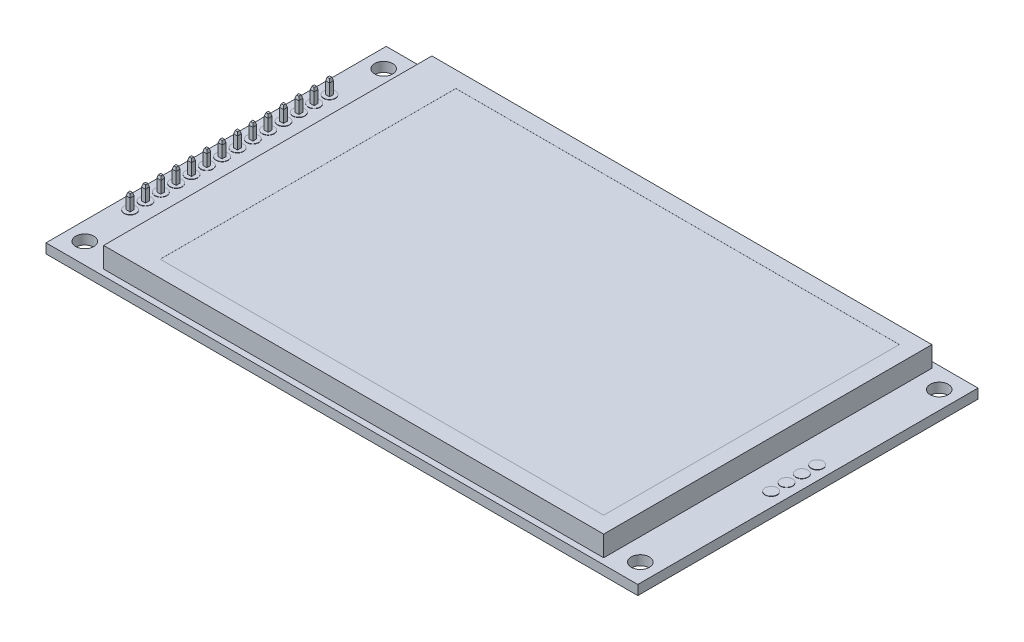
SolidWorks part; units mm, degrees
ref_plane "Front Plane" through (0, 0, 0) normal (0, 0, 1) x (1, 0, 0)
ref_plane "Top Plane" through (0, 0, 0) normal (0, 1, 0) x (1, 0, 0)
ref_plane "Right Plane" through (0, 0, 0) normal (1, 0, 0) x (0, 0, -1)
sketch "Sketch1" plane through (0, 0, 0) normal (0, 1, 0) x (1, 0, 0)
  line L1 (-49, 28.17) -> (49, 28.17)
  line L2 (-49, 28.17) -> (-49, -28.17)
  line L3 (-49, -28.17) -> (49, -28.17)
  line L4 (49, 28.17) -> (49, -28.17)
  line L5 (-49, 28.17) -> (49, -28.17) construction
  line L6 (-49, -28.17) -> (49, 28.17) construction
  point P0 (0, 0)
  dimension "D1" = 98
  dimension "D2" = 56.34
extrude "Boss-Extrude1" add sketch "Sketch1" along normal blind 1.6
sketch "Sketch2" plane through (0, 1.6, 0) normal (0, 1, 0) x (1, 0, 0)
  line L0 (0, 35.5842) -> (0, -40.7183) construction
  line L1 (-57.8022, 0) -> (54.4386, 0) construction
  line L2 (-49, 28.17) -> (-49, -28.17) construction
  line L3 (49, 28.17) -> (-49, 28.17) construction
  circle A0 centre (-46, 24.75) radius 1.5
  circle A1 centre (46, 24.75) radius 1.5
  circle A2 centre (46, -24.75) radius 1.5
  circle A3 centre (-46, -24.75) radius 1.5
  dimension "D1" = 3
  dimension "D2" = 3.42
extrude "Cut-Extrude1" cut sketch "Sketch2" against normal blind 1.6
sketch "Sketch3" plane through (0, 1.6, 0) normal (0, 1, 0) x (1, 0, 0)
  line L0 (-49, 28.17) -> (-49, -28.17) construction
  line L1 (-49, -28.17) -> (49, -28.17) construction
  circle A0 centre (-46.73, -16.51) radius 1
  circle A1 centre (-46.73, -13.97) radius 1
  circle A2 centre (-46.73, -11.43) radius 1
  circle A3 centre (-46.73, -8.89) radius 1
  circle A4 centre (-46.73, -6.35) radius 1
  circle A5 centre (-46.73, -3.81) radius 1
  circle A6 centre (-46.73, -1.27) radius 1
  circle A7 centre (-46.73, 1.27) radius 1
  circle A8 centre (-46.73, 3.81) radius 1
  circle A9 centre (-46.73, 6.35) radius 1
  circle A10 centre (-46.73, 8.89) radius 1
  circle A11 centre (-46.73, 11.43) radius 1
  circle A12 centre (-46.73, 13.97) radius 1
  circle A13 centre (-46.73, 16.51) radius 1
  dimension "D1" = 2.27
  dimension "D2" = 11.66
  dimension "D3" = 14
extrude "Boss-Extrude2" add sketch "Sketch3" along normal blind 0.05
sketch "Sketch4" plane through (0, 0, 0) normal (0, -1, 0) x (1, 0, 0)
  line L0 (-49, 28.17) -> (49, 28.17) construction
  line L1 (-45.46, -17.8) -> (-48, -17.8)
  line L2 (-45.46, -17.8) -> (-45.46, 17.8)
  line L3 (-45.46, 17.8) -> (-48, 17.8)
  line L4 (-48, -17.8) -> (-48, 17.8)
  line L5 (-49, -28.17) -> (-49, 28.17) construction
  dimension "D1" = 2.54
  dimension "D2" = 35.6
  dimension "D3" = 10.37
  dimension "D4" = 1
extrude "Boss-Extrude3" add sketch "Sketch4" along normal blind 2.54
sketch "Sketch5" plane through (0, 1.6, 0) normal (0, 1, 0) x (1, 0, 0)
  line L0 (49, -28.17) -> (49, 28.17) construction
  line L1 (-49, -28.17) -> (49, -28.17) construction
  circle A0 centre (46.73, -3.81) radius 1
  circle A1 centre (46.73, -1.27) radius 1
  circle A2 centre (46.73, 1.27) radius 1
  circle A3 centre (46.73, 3.81) radius 1
  dimension "D1" = 2.27
  dimension "D2" = 24.36
  dimension "D3" = 4
extrude "Boss-Extrude4" add sketch "Sketch5" along normal blind 0.05 and the other way blind 1.65
sketch "Sketch6" plane through (0, 1.6, 0) normal (0, 1, 0) x (1, 0, 0)
  line L1 (-47.055, -16.185) -> (-46.405, -16.185)
  line L2 (-47.055, -16.185) -> (-47.055, -16.835)
  line L3 (-47.055, -16.835) -> (-46.405, -16.835)
  line L4 (-46.405, -16.185) -> (-46.405, -16.835)
  line L5 (-47.055, -16.185) -> (-46.405, -16.835) construction
  line L6 (-47.055, -16.835) -> (-46.405, -16.185) construction
  point P0 (-46.73, -16.51)
  dimension "D1" = 0.65
  dimension "D2" = 0.65
extrude "Boss-Extrude5" add sketch "Sketch6" along normal blind 2.04 and the other way blind 9.5
sketch "Sketch7" plane through (0, 3.64, 0) normal (0, 1, 0) x (1, 0, 0)
  line L1 (-47.055, -16.185) -> (-46.405, -16.185)
  line L2 (-47.055, -16.185) -> (-47.055, -16.835)
  line L3 (-47.055, -16.835) -> (-46.405, -16.835)
  line L4 (-46.405, -16.185) -> (-46.405, -16.835)
extrude "Boss-Extrude6" add sketch "Sketch7" along normal blind 0.5 draft 15
sketch "Sketch8" plane through (0, -7.9, 0) normal (0, -1, 0) x (1, 0, 0)
  line L1 (-46.405, 16.185) -> (-47.055, 16.185)
  line L2 (-46.405, 16.185) -> (-46.405, 16.835)
  line L3 (-46.405, 16.835) -> (-47.055, 16.835)
  line L4 (-47.055, 16.185) -> (-47.055, 16.835)
extrude "Boss-Extrude7" add sketch "Sketch8" along normal blind 0.5 draft 15
pattern_linear "LPattern1" count 14 spacing 2.54 along (0, 0, -1) of "Boss-Extrude5", "Boss-Extrude7", "Boss-Extrude6"
sketch "Sketch9" plane through (0, 1.6, 0) normal (0, 1, 0) x (1, 0, 0)
  line L0 (-49, 28.17) -> (-49, -28.17) construction
  line L1 (-40.45, 27.18) -> (42.35, 27.18)
  line L2 (-40.45, 27.18) -> (-40.45, -27.17)
  line L3 (-40.45, -27.17) -> (42.35, -27.17)
  line L4 (42.35, 27.18) -> (42.35, -27.17)
  line L6 (-49, -28.17) -> (49, -28.17) construction
  dimension "D1" = 54.35
  dimension "D2" = 82.8
  dimension "D3" = 8.55
  dimension "D4" = 1
extrude "Boss-Extrude8" add sketch "Sketch9" along normal blind 2.3
sketch "Sketch10" plane through (0, 3.9, 0) normal (0, 1, 0) x (1, 0, 0)
  line L1 (-40.45, 27.18) -> (42.35, 27.18)
  line L2 (-40.45, 27.18) -> (-40.45, -27.17)
  line L3 (-40.45, -27.17) -> (42.35, -27.17)
  line L4 (42.35, 27.18) -> (42.35, -27.17)
extrude "Boss-Extrude9" add sketch "Sketch10" along normal blind 1.1
sketch "Sketch11" plane through (0, 5, 0) normal (0, 1, 0) x (1, 0, 0)
  line L0 (-40.45, -27.17) -> (42.35, -27.17) construction
  line L1 (-33.795, 24.495) -> (39.645, 24.495)
  line L2 (-33.795, 24.495) -> (-33.795, -24.465)
  line L3 (-33.795, -24.465) -> (39.645, -24.465)
  line L4 (39.645, 24.495) -> (39.645, -24.465)
  line L5 (42.35, -27.17) -> (42.35, 27.18) construction
  dimension "D1" = 73.44
  dimension "D2" = 48.96
  dimension "D3" = 2.705
  dimension "D4" = 2.705
extrude "Cut-Extrude2" cut sketch "Sketch11" against normal blind 0.01
sketch "Sketch12" plane through (0, 0, 0) normal (0, -1, 0) x (1, 0, 0)
  line L0 (49, 28.17) -> (49, -28.17) construction
  line L1 (29.4, -25.87) -> (2.8, -25.87)
  line L2 (29.4, -25.87) -> (29.4, -9.17)
  line L3 (29.4, -9.17) -> (2.8, -9.17)
  line L4 (2.8, -25.87) -> (2.8, -9.17)
  line L5 (49, -28.17) -> (-49, -28.17) construction
  dimension "D1" = 26.6
  dimension "D2" = 16.7
  dimension "D3" = 19.6
  dimension "D4" = 2.3
extrude "Boss-Extrude10" add sketch "Sketch12" along normal blind 2.9
sketch "Sketch13" plane through (0, -2.9, 0) normal (0, -1, 0) x (1, 0, 0)
  line L0 (27.4, -9.17) -> (27.4, -14.17)
  line L1 (29.4, -9.17) -> (2.8, -9.17) construction
  line L2 (27.4, -14.17) -> (29.4, -16.97)
  line L4 (29.4, -16.97) -> (29.4, -9.17)
  line L5 (29.4, -9.17) -> (27.4, -9.17)
  dimension "D1" = 2
  dimension "D2" = 7.8
  dimension "D3" = 5
extrude "Cut-Extrude3" cut sketch "Sketch13" against normal blind 2.9
